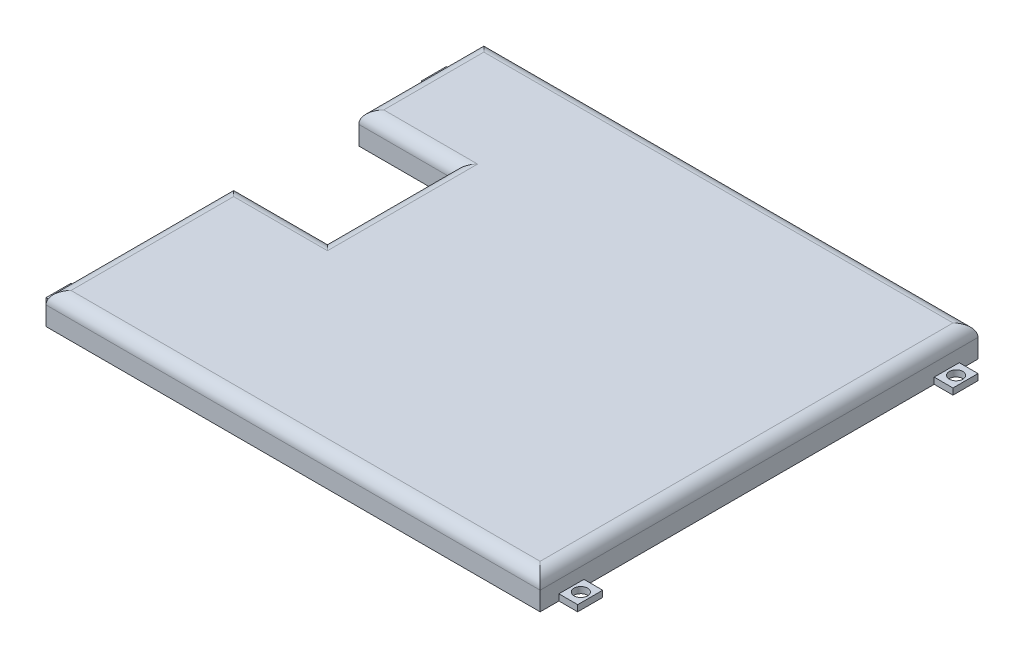
SolidWorks part; units mm, degrees
ref_plane "Front Plane" through (0, 0, 0) normal (0, 0, 1) x (1, 0, 0)
ref_plane "Top Plane" through (0, 0, 0) normal (0, 1, 0) x (1, 0, 0)
ref_plane "Right Plane" through (0, 0, 0) normal (1, 0, 0) x (0, 0, -1)
sketch "Sketch2" plane through (0, 0, 0) normal (0, 1, 0) x (1, 0, 0)
  line L0 (0, 0) -> (79, 0)
  line L1 (79, 0) -> (79, 70)
  line L2 (79, 70) -> (0, 70)
  line L3 (0, 70) -> (0, 50)
  line L4 (0, 50) -> (15, 50)
  line L5 (15, 50) -> (15, 30)
  line L6 (15, 30) -> (0, 30)
  line L7 (0, 30) -> (0, 0)
  dimension "D1" = 79
  dimension "D2" = 70
  dimension "D3" = 20
  dimension "D4" = 20
  dimension "D5" = 15
extrude "Boss-Extrude1" add sketch "Sketch2" along normal blind 5
sketch "Sketch3" plane through (79, 0, 0) normal (1, 0, 0) x (0, 0, -1)
  line L0 (0, 5) -> (70, 5) construction
  line L1 (3, 5) -> (7, 5)
  line L2 (3, 5) -> (3, 0)
  line L3 (3, 0) -> (7, 0)
  line L4 (7, 5) -> (7, 0)
  line L5 (0, 0) -> (70, 0) construction
  line L6 (0, 5) -> (0, 0) construction
  dimension "D1" = 4
  dimension "D2" = 3
extrude "Boss-Extrude2" add sketch "Sketch3" along normal blind 3
sketch "Sketch4" plane through (0, 5, 0) normal (0, 1, 0) x (1, 0, 0)
  line L0 (82, 7) -> (82, 3) construction
  line L1 (82, 7) -> (79, 7) construction
  circle A0 centre (80.5, 5) radius 1.08
  dimension "D3" = 2.16
  dimension "D1" = 1.5
  dimension "D2" = 2
extrude "Cut-Extrude1" cut sketch "Sketch4" against normal through all
pattern_linear "LPattern1" count 2 spacing 60 along (0, 0, -1) count 2 spacing 82 along (-1, 0, 0) of "Boss-Extrude2"
pattern_linear "LPattern2" count 2 spacing 60 along (0, 0, -1) count 2 spacing 82 along (-1, 0, 0) of "Cut-Extrude1"
sketch "Sketch5" plane through (0, 5, 0) normal (0, 1, 0) x (1, 0, 0)
  line L1 (-3, 67) -> (0, 67)
  line L2 (-3, 67) -> (-3, 63)
  line L3 (-3, 63) -> (0, 63)
  line L4 (0, 67) -> (0, 63)
  line L5 (-3, 7) -> (0, 7)
  line L6 (-3, 7) -> (-3, 3)
  line L7 (-3, 3) -> (0, 3)
  line L8 (0, 7) -> (0, 3)
  line L9 (79, 7) -> (82, 7)
  line L10 (79, 7) -> (79, 3)
  line L11 (79, 3) -> (82, 3)
  line L12 (82, 7) -> (82, 3)
  line L13 (79, 67) -> (82, 67)
  line L14 (79, 67) -> (79, 63)
  line L15 (79, 63) -> (82, 63)
  line L16 (82, 67) -> (82, 63)
extrude "Cut-Extrude2" cut sketch "Sketch5" against normal blind 4
sketch "Sketch6" plane through (0, 0, 0) normal (0, -1, 0) x (1, 0, 0)
  line L0 (0, 0) -> (79, 0)
  line L1 (79, 0) -> (79, -70)
  line L2 (79, -70) -> (0, -70)
  line L3 (0, -70) -> (0, -50)
  line L4 (0, -50) -> (15, -50)
  line L5 (15, -50) -> (15, -30)
  line L6 (15, -30) -> (0, -30)
  line L7 (0, -30) -> (0, 0)
  line L8 (2, -28) -> (2, -2)
  line L9 (2, -2) -> (77, -2)
  line L10 (77, -2) -> (77, -68)
  line L11 (77, -68) -> (2, -68)
  line L12 (2, -68) -> (2, -52)
  line L13 (2, -52) -> (17, -52)
  line L14 (17, -52) -> (17, -28)
  line L15 (17, -28) -> (2, -28)
  dimension "D1" = 2
sketch "Sketch7" plane through (0, 0, 0) normal (0, -1, 0) x (1, 0, 0)
  line L0 (2, -2) -> (77, -2)
  line L1 (77, -2) -> (77, -68)
  line L2 (77, -68) -> (2, -68)
  line L3 (2, -68) -> (2, -52)
  line L4 (2, -52) -> (17, -52)
  line L5 (17, -52) -> (17, -28)
  line L6 (17, -28) -> (2, -28)
  line L7 (2, -28) -> (2, -2)
extrude "Cut-Extrude3" cut sketch "Sketch7" against normal blind 4
fillet "Fillet1" radius 2 8 edges at (39.5, 5, 0) (0, 5, -15) (7.5, 5, -30) (15, 5, -40) (7.5, 5, -50) (0, 5, -60) (39.5, 5, -70) (79, 5, -35)
